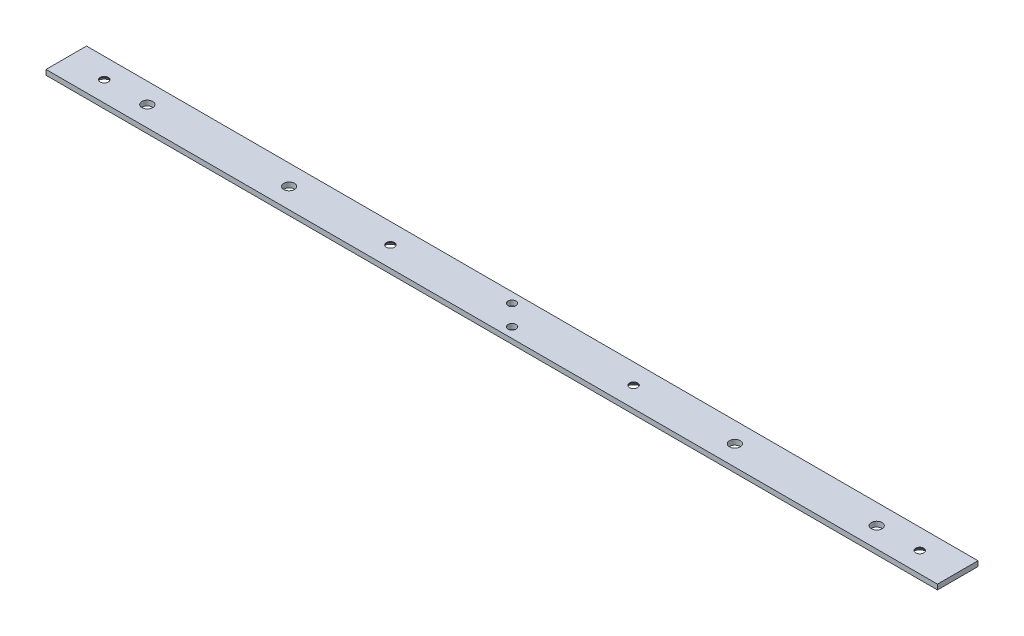
SolidWorks part; units mm, degrees
material "Copper"
ref_plane "Front Plane" through (0, 0, 0) normal (0, 0, 1) x (1, 0, 0)
ref_plane "Top Plane" through (0, 0, 0) normal (0, 1, 0) x (1, 0, 0)
ref_plane "Right Plane" through (0, 0, 0) normal (1, 0, 0) x (0, 0, -1)
sketch "Sketch1" plane through (0, 0, 0) normal (1, 0, 0) x (0, 0, -1)
  line L1 (-12.7, 1.5875) -> (12.7, 1.5875)
  line L2 (-12.7, 1.5875) -> (-12.7, -1.5875)
  line L3 (-12.7, -1.5875) -> (12.7, -1.5875)
  line L4 (12.7, 1.5875) -> (12.7, -1.5875)
  line L5 (-12.7, 1.5875) -> (12.7, -1.5875) construction
  line L6 (-12.7, -1.5875) -> (12.7, 1.5875) construction
  point P0 (0, 0)
  dimension "D1" = 3.175
  dimension "D2" = 25.4
extrude "Boss-Extrude1" add sketch "Sketch1" along normal mid plane 558.8
hole_wizard "1/4 Clearance Hole1" positions "Sketch2" profile "Sketch3" hole size "1/4" standard "ANSI Inch" end condition through all
sketch "Sketch2" plane through (0, 1.5875, 0) normal (0, 1, 0) x (1, 0, 0)
  line L0 (-273.05, 4.8257) -> (-184.15, 4.8257)
  line L1 (-184.15, 4.8257) -> (-95.25, 4.8257)
  line L4 (-279.4, 12.7) -> (-279.4, -12.7) construction
  line L5 (-273.05, 4.8257) -> (-228.6, 0) construction
  line L6 (-228.6, 0) -> (-184.15, 4.8257) construction
  line L8 (-139.7, 0) -> (-184.15, 4.8257) construction
  line L10 (-139.7, 0) -> (-95.25, 4.8257) construction
  line L12 (279.4, -12.7) -> (-279.4, -12.7) construction
  point P12 (-228.6, 0)
  point P14 (-139.7, 0)
  dimension "D1" = 6.35
  dimension "D2" = 88.9
  dimension "D3" = 88.9
  dimension "D4" = 12.7
sketch "Sketch3" plane through (-139.7, 1.5875, 0) normal (1, 0, 0) x (0, 0, 1)
  line L0 (0, 0) -> (0, 3.175)
  line L1 (0, 3.175) -> (3.3782, 3.175)
  line L2 (3.3782, 3.175) -> (3.3782, 0)
  line L5 (3.3782, 0) -> (0, 0)
  line L11 (0, -6.35) -> (0, 107.95) construction
  dimension "Thru Hole Dia." = 6.7564
  dimension "Thru Hole Depth" = 3.175
mirror "Mirror1" about plane through (0, 0, 0) normal (1, 0, 0) of "1/4 Clearance Hole1"
hole_wizard "#10 Clearance Hole1" positions "Sketch4" profile "Sketch5" hole size "#10" standard "ANSI Inch" end condition through all
sketch "Sketch4" plane through (0, 1.5875, 0) normal (0, 1, 0) x (1, 0, 0)
  point P0 (6.35, -6.35)
  point P2 (-6.35, 6.35)
  dimension "D1" = 6.35
  dimension "D2" = 6.35
  dimension "D3" = 6.35
  dimension "D4" = 6.35
sketch "Sketch5" plane through (6.35, 1.5875, 6.35) normal (1, 0, 0) x (0, 0, 1)
  line L0 (0, 0) -> (0, 3.175)
  line L1 (0, 3.175) -> (2.5527, 3.175)
  line L2 (2.5527, 3.175) -> (2.5527, 0)
  line L5 (2.5527, 0) -> (0, 0)
  line L11 (0, -6.35) -> (0, 107.95) construction
  dimension "Thru Hole Dia." = 5.1054
  dimension "Thru Hole Depth" = 3.175
hole_wizard "CSK for #10 Flat Head Machine Screw1" positions "Sketch6" profile "Sketch7" countersink size "#10" standard "ANSI Inch" end condition through all
sketch "Sketch6" plane through (0, -1.5875, -101.6) normal (0, -1, 0) x (-1, 0, 0)
  point P0 (76.2, -101.6)
  point P3 (76.2, -50.8)
  point P6 (255.5875, -50.8)
  point P9 (255.5875, -101.6)
  point P12 (-255.5875, -101.6)
  point P15 (-76.2, -101.6)
  point P18 (-76.2, -50.8)
  point P21 (-255.5875, -50.8)
sketch "Sketch7" plane through (-76.2, -1.5875, 0) normal (1, 0, 0) x (0, 0, -1)
  line L0 (0, 0) -> (0, 3.175)
  line L1 (0, 3.175) -> (2.5527, 3.175)
  line L2 (2.5527, 3.175) -> (2.5527, 2.6882)
  line L3 (2.5527, 2.6882) -> (4.8895, 0)
  line L4 (4.8895, 0) -> (0, 0)
  line L5 (-2.5527, 2.6882) -> (-4.8895, 0) construction
  line L6 (0, -6.35) -> (0, 107.95) construction
  dimension "Thru Hole Dia." = 5.1054
  dimension "Thru Hole Depth" = 3.175
  dimension "Near C'Sink Dia." = 9.779
  dimension "Near C'Sink Angle" = 82
